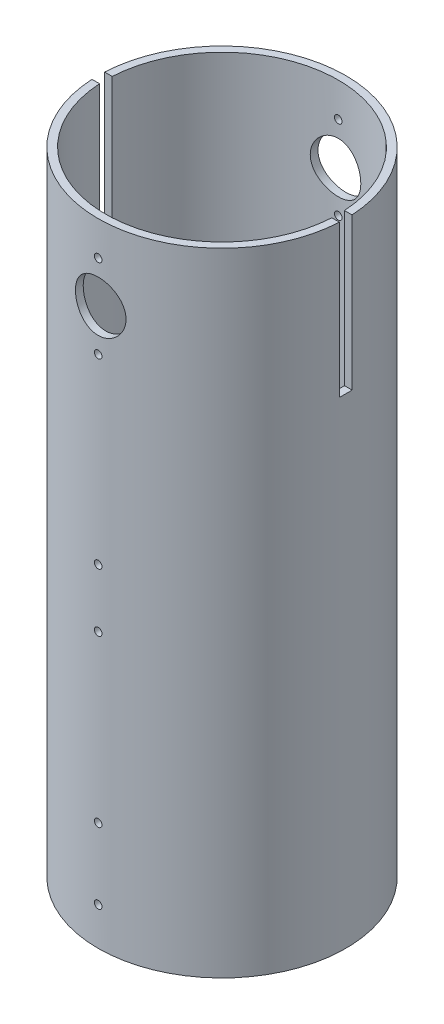
SolidWorks part; units mm, degrees
ref_plane "Front Plane" through (0, 0, 0) normal (0, 0, 1) x (1, 0, 0)
ref_plane "Top Plane" through (0, 0, 0) normal (0, 1, 0) x (1, 0, 0)
ref_plane "Right Plane" through (0, 0, 0) normal (1, 0, 0) x (0, 0, -1)
sketch "Sketch7" plane through (0, 0, 0) normal (0, 1, 0) x (1, 0, 0)
  circle A0 centre (0, 0) radius 46
  circle A1 centre (0, 0) radius 49
  dimension "D1" = 92
  dimension "D2" = 98
extrude "Boss-Extrude3" add sketch "Sketch7" along normal blind 250
sketch "Sketch8" plane through (0, 0, 0) normal (0, 0, 1) x (1, 0, 0)
  line L0 (0, 0) -> (0, 15) construction
  line L1 (-49, 0) -> (49, 0) construction
  line L2 (0, 0) -> (0, 43) construction
  line L3 (0, 0) -> (0, 108.5) construction
  line L4 (0, 0) -> (0, 131.5) construction
  line L5 (0, 250) -> (0, 236.5) construction
  line L6 (49, 250) -> (-49, 250) construction
  line L7 (0, 250) -> (0, 220) construction
  line L8 (0, 250) -> (0, 203.5) construction
  circle A0 centre (0, 15) radius 1.5
  circle A1 centre (0, 43) radius 1.5
  circle A2 centre (0, 108.5) radius 1.5
  circle A3 centre (0, 131.5) radius 1.5
  circle A4 centre (0, 236.5) radius 1.5
  circle A5 centre (0, 203.5) radius 1.5
  circle A6 centre (0, 220) radius 10
  dimension "D8" = 3
  dimension "D9" = 3
  dimension "D10" = 3
  dimension "D11" = 3
  dimension "D12" = 3
  dimension "D13" = 3
  dimension "D14" = 20
  dimension "D1" = 15
  dimension "D2" = 43
  dimension "D3" = 108.5
  dimension "D4" = 131.5
  dimension "D5" = 13.5
  dimension "D6" = 30
  dimension "D7" = 46.5
extrude "Cut-Extrude4" cut sketch "Sketch8" against normal through all and the other way through all
sketch "Sketch9" plane through (0, 0, 0) normal (1, 0, 0) x (0, 0, -1)
  line L0 (0, 250) -> (0, 190) construction
  line L1 (49, 250) -> (-49, 250) construction
  line L2 (-2.5, 250) -> (-2.5, 190)
  line L3 (2.5, 250) -> (2.5, 190)
  line L4 (-2.5, 250) -> (2.5, 250)
  line L5 (-2.5, 190) -> (2.5, 190)
  dimension "D1" = 60
  dimension "D2" = 2.5
  dimension "D3" = 2.5
extrude "Cut-Extrude5" cut sketch "Sketch9" against normal through all and the other way through all
